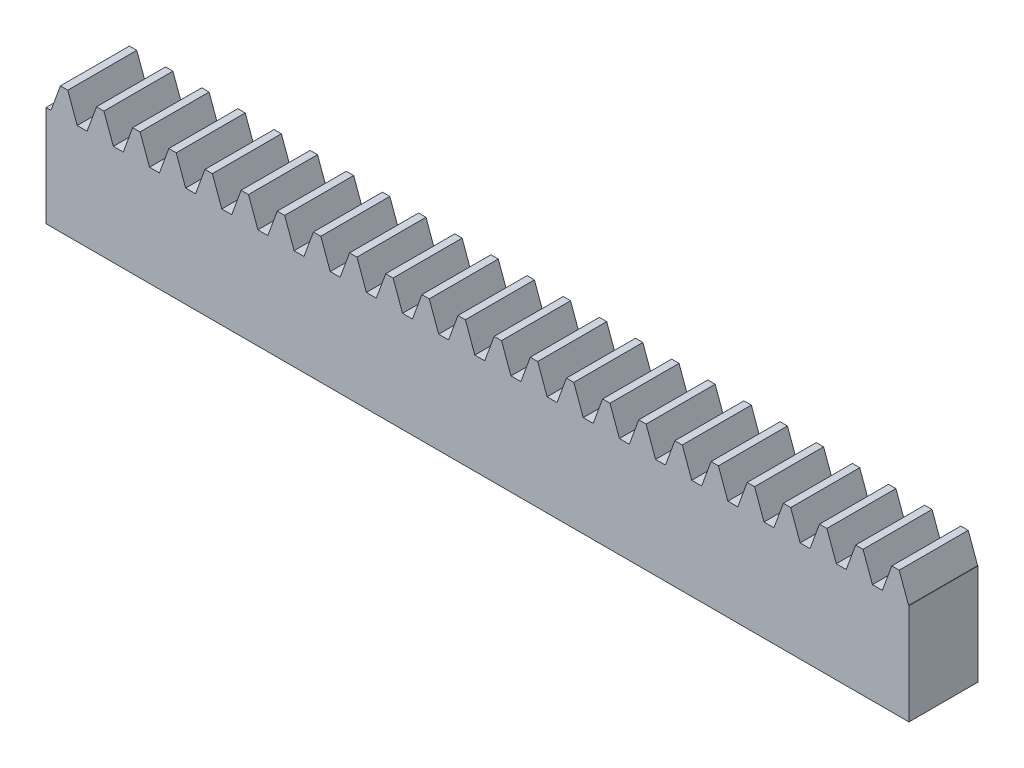
SolidWorks part; units mm, degrees
extrude "Blank" add sketch "BlankSke" against normal blind 12
sketch "BlankSke" plane through (0, 0, 0) normal (0, 0, 1) x (1, 0, 0)
  line L1 (0, 0) -> (150, 0)
  line L2 (0, 0) -> (0, 22)
  line L3 (0, 22) -> (150, 22)
  line L4 (150, 0) -> (150, 22)
  dimension "Length" = 150
  dimension "Blank_height" = 22
ref_plane "Plane1" through (0, 0, 0) normal (0, 0, 1) x (1, 0, 0)
ref_plane "Plane2" through (0, 0, 0) normal (0, 1, 0) x (1, 0, 0)
ref_plane "Plane3" through (0, 0, 0) normal (1, 0, 0) x (0, 0, -1)
sketch "HoldingSke" plane through (0, 0, 0) normal (0, 1, 0) x (1, 0, 0)
  line L0 (0, 0) -> (0.0696, 0.4951)
  line L1 (-15, 0) -> (100, 0) construction
  line L2 (0, 0) -> (-2.1039, 2.3779)
  line L3 (0, 0) -> (-11.863, 4.5341)
  line L4 (0, 0) -> (7.8269, 3.6497)
  line L5 (0, 0) -> (-23.7986, -8.8762)
  line L6 (0, 0) -> (-10.5278, -7.1032)
  line L9 (-71.009, 38.7566) -> (69.9449, 90.0596)
  line L10 (-76.2, 4.3779) -> (-56.2, 4.3779)
  line L11 (0, 0) -> (-12, 0)
  line L12 (-76.2, 101.6) -> (-76.133, 101.6)
  line L13 (24.9733, 27.94) -> (52.9518, 28.4284)
  line L14 (24.9733, 27.94) -> (24.9743, 27.94)
  line L15 (24.9733, 27.94) -> (100.4006, 29.5858)
  circle A0 centre (0, 0) radius 19.05
  circle A1 centre (0, 0) radius 10
  circle A2 centre (0, 0) radius 12.7
  dimension "MPH" = 20
  dimension "Diameter" = 38.1
  dimension "Num_teeth" = 25
  dimension "Pitch" = 0.5
  dimension "Show_teeth" = 998
  dimension "Thickness" = 12.7
  dimension "Ap" = 20
  dimension "Pitch_height" = 20
  dimension "Width" = 12
  dimension "Backlash" = 0.067
  dimension "Addendum_fac" = 1
  dimension "Dedendum_fac" = 1.25
  dimension "Clearance_fac" = 0.25
  dimension "Dedendum_add" = 0.001
  dimension "Length" = 150
  dimension "Module" = 2
sketch "TooCutSkeIll" plane through (0, 0, 0) normal (0, 0, 1) x (1, 0, 0)
  line L0 (-2.4806, 21.9474) -> (-0.9819, 17.8296)
  line L1 (-0.5111, 17.5) -> (0.5111, 17.5)
  line L2 (0.9819, 17.8296) -> (2.4806, 21.9474)
  line L3 (150, 22) -> (0, 22) construction
  line L4 (0, 0) -> (0, 64.897) construction
  line L5 (-13.208, 20) -> (12.954, 20) construction
  line L6 (0, 0) -> (150, 0) construction
  line L7 (1.7718, 20) -> (1.7718, 48.7463) construction
  line L8 (-1.7718, 20) -> (-1.7718, 48.7463) construction
  line L9 (2.5558, 22) -> (2.5558, 22.0254)
  line L10 (-2.5558, 22) -> (-2.5558, 22.0254)
  line L11 (-2.5558, 22.0254) -> (2.5558, 22.0254)
  arc A0 (0.5111, 17.5) -> (0.9819, 17.8296) centre (0.5111, 18.001) ccw
  arc A1 (-0.9819, 17.8296) -> (-0.5111, 17.5) centre (-0.5111, 18.001) ccw
  arc A2 (2.5558, 22) -> (2.4806, 21.9474) centre (2.5558, 21.92) ccw
  arc A3 (-2.4806, 21.9474) -> (-2.5558, 22) centre (-2.5558, 21.92) ccw
  dimension "Pitch_height" = 20
  dimension "Addendum_plus" = 2.0254
  dimension "Pressure_angle" = 20
  dimension "Gap_width" = 3.5436
  dimension "Dedendum" = 2.5
extrude "ToothCutIll" [suppressed] cut sketch "TooCutSkeIll" against normal through all
sketch "TooCutSkeSim" plane through (0, 0, 0) normal (0, 0, 1) x (1, 0, 0)
  line L0 (0.8619, 17.5) -> (-0.8619, 17.5)
  line L1 (2.509, 22.0254) -> (0.8619, 17.5)
  line L2 (0, 17.4625) -> (0, 53.467) construction
  line L3 (2.509, 22.0254) -> (-2.509, 22.0254)
  line L6 (-2.509, 22.0254) -> (-0.8619, 17.5)
  line L9 (-1.7718, 20) -> (1.7718, 20) construction
  line L10 (0, 0) -> (150, 0) construction
  line L11 (1.7718, 20) -> (1.7718, 53.467) construction
  line L12 (-1.7718, 20) -> (-1.7718, 53.467) construction
  dimension "Pitch_height" = 20
  dimension "Addendum_plus" = 2.0254
  dimension "Pressure_angle" = 20
  dimension "Gap_width" = 3.5436
  dimension "Dedendum" = 2.5
extrude "ToothCutSim" cut sketch "TooCutSkeSim" against normal through all
pattern_linear "TeethCuts" count 25 spacing 6.2832 along (1, 0, 0) of "ToothCutIll", "ToothCutSim"
equation "' \"Module@HoldingSke\" = 6.35"
equation "' \"Num_teeth@HoldingSke\" = 12"
equation "' \"Ap@HoldingSke\" =  20"
equation "' \"Ap@HoldingSke\" = 20"
equation "' \"Width@HoldingSke\" = 0.25 * 25.4"
equation "' \"Show_teeth@HoldingSke\" = 500"
equation "' \"Backlash@HoldingSke\" = 0.009 * 25.4"
equation "' \"Addendum_fac@HoldingSke\" = 1.0"
equation "' \"Dedendum_fac@HoldingSke\" = 1.25"
equation "' \"Dedendum_add@HoldingSke\" = 0.00005 * 25.4"
equation "' \"Clearance_fac@HoldingSke\" = 0.25"
equation "' \"Pitch_height@HoldingSke\" = 1 * 25.4"
equation "' \"Length@HoldingSke\" = 4.71 * 25.4"
equation "\"Pitch@HoldingSke\" = 1 / \"Module@HoldingSke\""
equation "\"MPH@HoldingSke\" = \"Dedendum_fac@HoldingSke\" / \"Pitch@HoldingSke\" + 2 * \"Dedendum_add@HoldingSke\" + 0.002 * 25.4"
equation "\"MPH@HoldingSke\" = ((sgn( \"MPH@HoldingSke\" - \"Pitch_height@HoldingSke\")+1)*( \"MPH@HoldingSke\" - \"Pitch_height@HoldingSke\"))/2 + \"Pitch_height@HoldingSke\""
equation "\"Blank_height@BlankSke\" = \"Pitch_height@HoldingSke\" + \"Addendum_fac@HoldingSke\"  / \"Pitch@HoldingSke\" "
equation "\"Length@BlankSke\" =  \"Length@HoldingSke\""
equation "\"Face_width@Blank\" = \"Width@HoldingSke\""
equation "\"Pressure_angle@TooCutSkeIll\" = \"Ap@HoldingSke\""
equation "\"Addendum_plus@TooCutSkeIll\" =  \"Addendum_fac@HoldingSke\"  / \"Pitch@HoldingSke\" + 0.001 *25.4"
equation "\"Dedendum@TooCutSkeIll\" = \"Dedendum_fac@HoldingSke\"  / \"Pitch@HoldingSke\""
equation "\"Pitch_height@TooCutSkeIll\" =  \"MPH@HoldingSke\""
equation "\"Gap_width@TooCutSkeIll\" = 3.14159265 / 2 / \"Pitch@HoldingSke\" + 6 * \"Backlash@HoldingSke\""
equation "\"Pressure_angle@TooCutSkeSim\" = \"Ap@HoldingSke\""
equation "\"Addendum_plus@TooCutSkeSim\" =  \"Addendum_fac@HoldingSke\"  / \"Pitch@HoldingSke\" + 0.001 * 25.4"
equation "\"Dedendum@TooCutSkeSim\" = \"Dedendum_fac@HoldingSke\"  / \"Pitch@HoldingSke\""
equation "\"Pitch_height@TooCutSkeSim\" =  \"MPH@HoldingSke\""
equation "\"Gap_width@TooCutSkeSim\" = 3.14159265 / 2 / \"Pitch@HoldingSke\" + 6 * \"Backlash@HoldingSke\""
equation "\"Root_fillet@TooCutSkeIll\" = \"Clearance_fac@HoldingSke\" / \"Pitch@HoldingSke\" + \"Dedendum_add@HoldingSke\""
equation "\"Break_rad@TooCutSkeIll\" = 0.02 / \"Pitch@HoldingSke\" * 2"
equation "\"Linear_pitch@TeethCuts\" = 3.14159265 / \"Pitch@HoldingSke\""
equation "\"Num_teeth@HoldingSke\" = int( ( \"Length@HoldingSke\" + 0 ) / (3.14159265 / \"Pitch@HoldingSke\")) + 0.9999  + 1"
equation " \"Num_teeth@TeethCuts\" = int( \"Show_teeth@HoldingSke\" ) + 1"
equation " \"Num_teeth@TeethCuts\" = ((sgn( \"Num_teeth@TeethCuts\" - \"Num_teeth@HoldingSke\" )-1)*( \"Num_teeth@TeethCuts\" - \"Num_teeth@HoldingSke\" ))/-2+ \"Num_teeth@HoldingSke\""
equation " \"Num_teeth@TeethCuts\" = ((sgn( \"Num_teeth@TeethCuts\" - 2.0)+1)*( \"Num_teeth@TeethCuts\" - 2.0))/2 +2.0"
